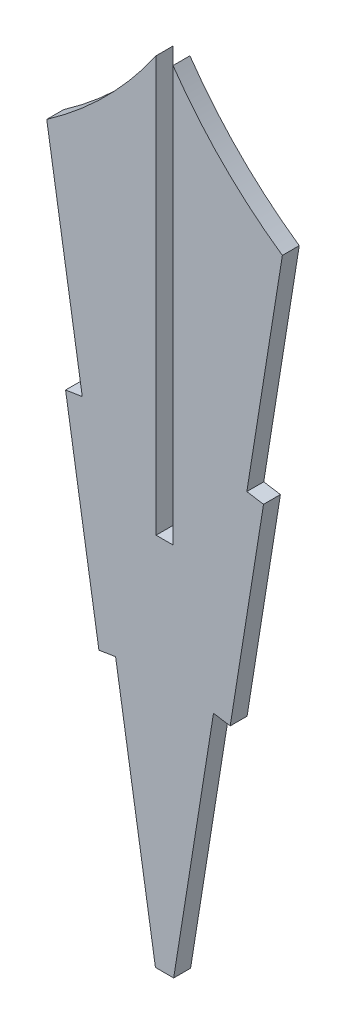
SolidWorks part; units mm, degrees
ref_plane "Front Plane" through (0, 0, 0) normal (0, 0, 1) x (1, 0, 0)
ref_plane "Top Plane" through (0, 0, 0) normal (0, 1, 0) x (1, 0, 0)
ref_plane "Right Plane" through (0, 0, 0) normal (1, 0, 0) x (0, 0, -1)
sketch "Sketch1" plane through (0, 0, 0) normal (0, 0, 1) x (1, 0, 0)
  line L0 (0, -185.0621) -> (-1.524, -185.0621)
  line L2 (-1.524, -185.0621) -> (-1.524, -147.6247)
  line L4 (-11.3846, -157.5214) -> (-8.1817, -177.5653)
  line L5 (-5.1757, -196.3766) -> (-1.5851, -218.846)
  line L6 (-8.1817, -177.5653) -> (-9.6866, -177.8058)
  line L7 (-5.1757, -196.3766) -> (-6.6806, -196.6171)
  line L8 (-0.762, -185.0621) -> (-0.762, -247.1656) construction
  line L9 (-9.6866, -177.8058) -> (-6.6806, -196.6171)
  line L10 (-1.5851, -218.846) -> (0.0611, -218.846)
  line L11 (8.1626, -177.8058) -> (5.1566, -196.6171)
  line L12 (3.6517, -196.3766) -> (5.1566, -196.6171)
  line L13 (6.6577, -177.5653) -> (8.1626, -177.8058)
  line L14 (3.6517, -196.3766) -> (0.0611, -218.846)
  line L15 (9.8606, -157.5214) -> (6.6577, -177.5653)
  line L16 (0, -185.0621) -> (0, -147.6247)
  arc A2 (-1.524, -147.6247) -> (-11.3846, -157.5214) centre (-33.7965, -125.3306) cw
  arc A3 (0, -147.6247) -> (9.8606, -157.5214) centre (32.2725, -125.3306) ccw
  point P0 (0, 0)
  point P21 (-0.762, -219.2285)
  point P26 (-0.762, -185.0621)
extrude "Boss-Extrude1" add sketch "Sketch1" along normal blind 1.524
